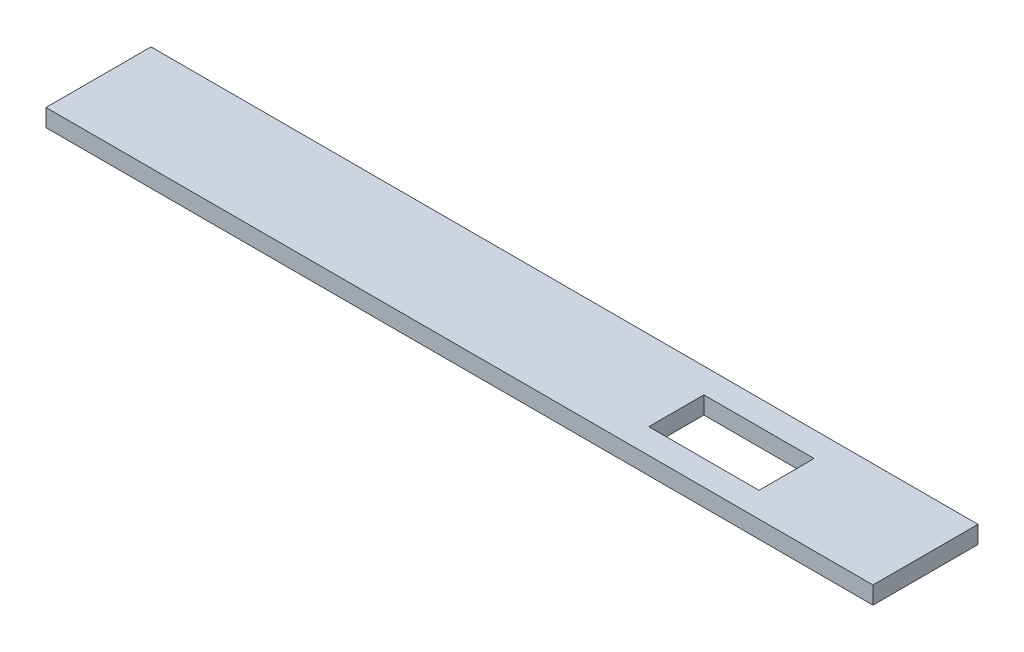
SolidWorks part; units mm, degrees
ref_plane "Front Plane" through (0, 0, 0) normal (0, 0, 1) x (1, 0, 0)
ref_plane "Top Plane" through (0, 0, 0) normal (0, 1, 0) x (1, 0, 0)
ref_plane "Right Plane" through (0, 0, 0) normal (1, 0, 0) x (0, 0, -1)
sketch "Sketch1" plane through (0, 0, -6.35) normal (0, 0, 1) x (1, 0, 0)
  line L1 (395.4432, 46.3301) -> (95.3421, 46.3301)
  line L2 (395.4432, 46.3301) -> (395.4432, 52.6801)
  line L3 (395.4432, 52.6801) -> (95.3421, 52.6801)
  line L4 (95.3421, 46.3301) -> (95.3421, 52.6801)
extrude "Boss-Extrude1" add sketch "Sketch1" along normal blind 38.1
sketch "Sketch2" plane through (0, 52.6801, 0) normal (0, 1, 0) x (1, 0, 0)
  line L1 (305.0269, -2.7) -> (345.0269, -2.7)
  line L2 (305.0269, -2.7) -> (305.0269, -22.7)
  line L3 (305.0269, -22.7) -> (345.0269, -22.7)
  line L4 (345.0269, -2.7) -> (345.0269, -22.7)
  line L12 (395.4432, 6.35) -> (95.3421, 6.35) construction
  line L13 (395.4432, -31.75) -> (95.3421, -31.75) construction
  dimension "D1" = 20
  dimension "D2" = 40
  dimension "D3" = 9.05
  dimension "D4" = 9.05
extrude "Cut-Extrude1" cut sketch "Sketch2" against normal through all
